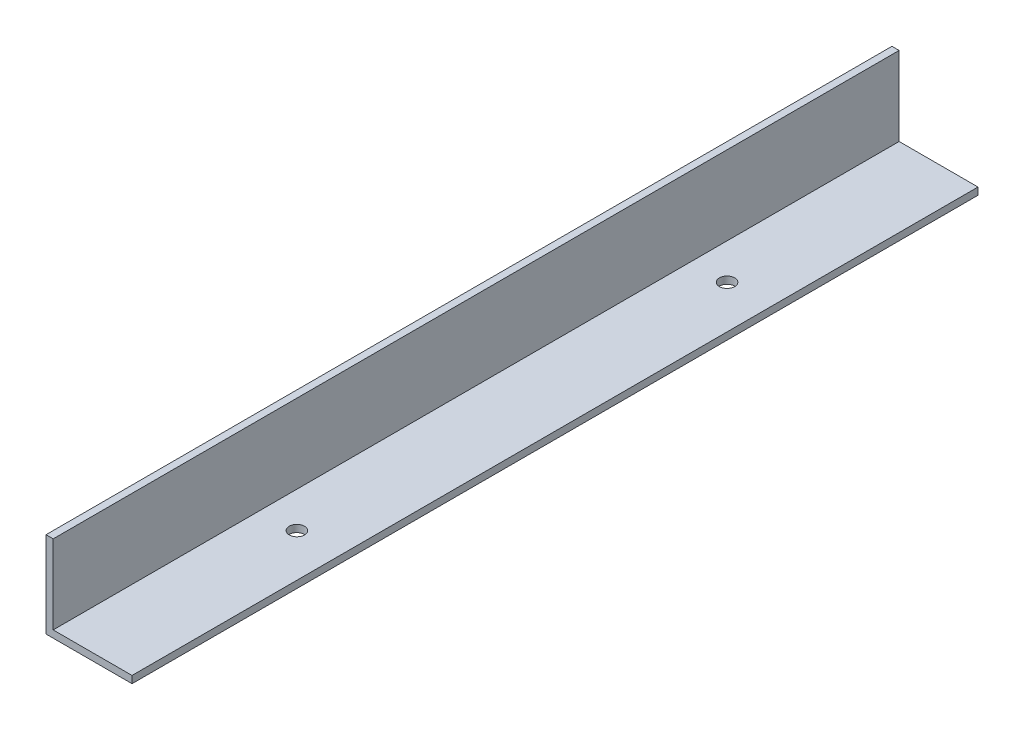
SolidWorks part; units mm, degrees
material "6061 Alloy"
ref_plane "Front Plane" through (0, 0, 0) normal (0, 0, 1) x (1, 0, 0)
ref_plane "Top Plane" through (0, 0, 0) normal (0, 1, 0) x (1, 0, 0)
ref_plane "Right Plane" through (0, 0, 0) normal (1, 0, 0) x (0, 0, -1)
sketch "Sketch1" plane through (0, 0, 0) normal (0, 0, 1) x (1, 0, 0)
  line L0 (0, 0) -> (0, 38.1)
  line L1 (0, 38.1) -> (3.175, 38.1)
  line L2 (3.175, 38.1) -> (3.175, 3.175)
  line L3 (3.175, 3.175) -> (38.1, 3.175)
  line L4 (38.1, 3.175) -> (38.1, 0)
  line L5 (38.1, 0) -> (0, 0)
  dimension "D1" = 38.1
  dimension "D2" = 3.175
extrude "Boss-Extrude1" add sketch "Sketch1" along normal blind 374.65
hole_wizard "1/4 Clearance Hole1" positions "Sketch2" profile "Sketch3" hole size "1/4" standard "ANSI Inch" end condition through all
sketch "Sketch2" plane through (0, 0, 0) normal (0, -1, 0) x (-1, 0, 0)
  line L0 (0, -374.65) -> (0, 0) construction
  line L1 (0, 0) -> (-38.1, 0) construction
  line L2 (0, -374.65) -> (-38.1, -374.65) construction
  point P0 (-19.05, -92.075)
  point P2 (-19.05, -282.575)
  dimension "D1" = 19.05
  dimension "D2" = 92.075
  dimension "D3" = 92.075
sketch "Sketch3" plane through (19.05, 0, 92.075) normal (1, 0, 0) x (0, 0, -1)
  line L0 (0, 0) -> (0, 38.1)
  line L1 (0, 38.1) -> (3.3782, 38.1)
  line L2 (3.3782, 38.1) -> (3.3782, 0)
  line L5 (3.3782, 0) -> (0, 0)
  line L11 (0, -6.35) -> (0, 107.95) construction
  dimension "Thru Hole Dia." = 6.7564
  dimension "Thru Hole Depth" = 38.1
